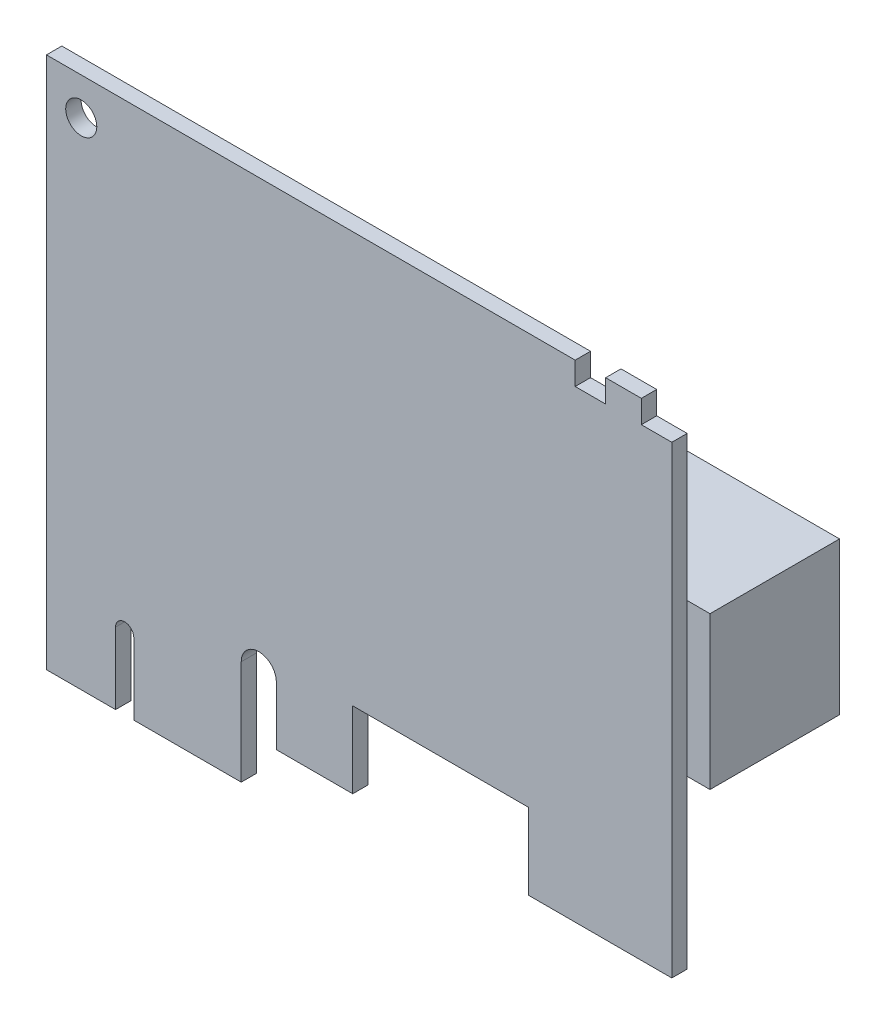
SolidWorks part; units mm, degrees
ref_plane "Front Plane" through (0, 0, 0) normal (0, 0, 1) x (1, 0, 0)
ref_plane "Top Plane" through (0, 0, 0) normal (0, 1, 0) x (1, 0, 0)
ref_plane "Right Plane" through (0, 0, 0) normal (1, 0, 0) x (0, 0, -1)
sketch "Sketch2" plane through (0, 0, 0) normal (0, 0, 1) x (1, 0, 0)
  line L1 (0, 0) -> (7.2, 0)
  line L2 (0, 0) -> (0, 55.5)
  line L3 (0, 55.5) -> (55.1064, 55.5)
  line L4 (65.1764, 4.7625) -> (65.1764, 53.1187)
  line L6 (7.2, 0) -> (7.2, 7.45)
  line L8 (9.1, 0) -> (9.1, 7.45)
  line L10 (20.3, 0) -> (20.3, 10.8712)
  line L12 (23.9576, 4.7625) -> (23.9576, 10.8712)
  line L13 (9.1, 0) -> (20.3, 0)
  line L14 (50.2593, 4.7625) -> (65.1764, 4.7625)
  line L16 (31.9205, 4.7625) -> (31.9205, 12.7)
  line L17 (31.9205, 12.7) -> (50.2593, 12.7)
  line L18 (50.2593, 4.7625) -> (50.2593, 12.7)
  line L19 (31.9205, 4.7625) -> (23.9576, 4.7625)
  line L23 (58.2814, 55.5) -> (62.0014, 55.5)
  line L25 (62.0014, 55.5) -> (62.0014, 53.1187)
  line L26 (62.0014, 53.1187) -> (65.1764, 53.1187)
  line L29 (55.1064, 55.5) -> (55.1064, 53.1187)
  line L30 (55.1064, 53.1187) -> (58.2814, 53.1187)
  line L31 (58.2814, 55.5) -> (58.2814, 53.1187)
  arc A0 (9.1, 7.45) -> (7.2, 7.45) centre (8.15, 7.45) ccw
  arc A1 (23.9576, 10.8712) -> (20.3, 10.8712) centre (22.1288, 10.8712) ccw
  circle A2 centre (3.625, 51.625) radius 1.6192
  point P12 (22.1288, 12.7)
  dimension "D7" = 4.7625
  dimension "D9" = 12.7
  dimension "D21" = 3.2385
  dimension "D2" = 55.5
  dimension "D3" = 20.3
  dimension "D4" = 3.6576
  dimension "D5" = 1.9
  dimension "D6" = 8.15
  dimension "D8" = 7.45
  dimension "D10" = 18.3388
  dimension "D11" = 7.9629
  dimension "D12" = 3.175
  dimension "D13" = 3.175
  dimension "D14" = 3.72
  dimension "D15" = 2.3812
  dimension "D16" = 65.1764
  dimension "D17" = 14.9171
  dimension "D18" = 7.2
  dimension "D19" = 11.2
  dimension "D20" = 42.8
  dimension "D22" = 3.625
  dimension "D23" = 3.875
extrude "Boss-Extrude1" add sketch "Sketch2" along normal blind 1.6
sketch "Sketch3" plane through (0, 0, 0) normal (0, 0, -1) x (-1, 0, 0)
  line L0 (-65.1764, 4.7625) -> (-65.1764, 53.1187) construction
  line L1 (-67.5576, 38.0375) -> (-45.3326, 38.0375)
  line L2 (-67.5576, 38.0375) -> (-67.5576, 22.1625)
  line L3 (-67.5576, 22.1625) -> (-45.3326, 22.1625)
  line L4 (-45.3326, 38.0375) -> (-45.3326, 22.1625)
  line L5 (-55.1064, 55.5) -> (0, 55.5) construction
  dimension "D1" = 2.3813
  dimension "D2" = 15.875
  dimension "D3" = 17.4625
  dimension "D4" = 22.225
extrude "Boss-Extrude2" add sketch "Sketch3" along normal blind 13.5
